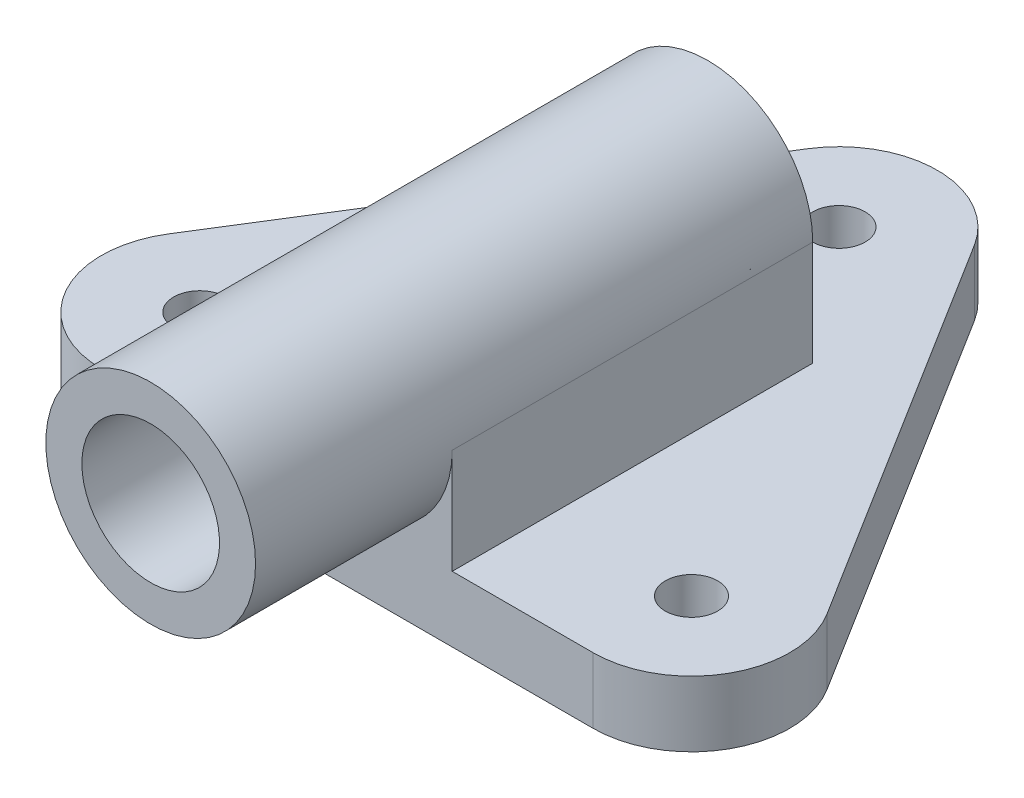
SolidWorks part; units mm, degrees
ref_plane "Front Plane" through (0, 0, 0) normal (0, 0, 1) x (1, 0, 0)
ref_plane "Top Plane" through (0, 0, 0) normal (0, 1, 0) x (1, 0, 0)
ref_plane "Right Plane" through (0, 0, 0) normal (1, 0, 0) x (0, 0, -1)
sketch "Sketch2" plane through (0, 0, 0) normal (0, 1, 0) x (1, 0, 0)
  line L0 (0, 0) -> (0, -4) construction
  line L1 (-50.22, -52.05) -> (-12.72, 7.95)
  line L2 (12.72, 7.95) -> (50.22, -52.05)
  line L3 (37.5, -75) -> (-37.5, -75)
  line L4 (0, -75) -> (0, -98.7993) construction
  arc A0 (12.72, 7.95) -> (-12.72, 7.95) centre (0, 0) ccw
  circle A1 centre (0, 0) radius 4
  arc A2 (-50.22, -52.05) -> (-37.5, -75) centre (-37.5, -60) ccw
  arc A3 (37.5, -75) -> (50.22, -52.05) centre (37.5, -60) ccw
  circle A4 centre (-37.5, -60) radius 4
  circle A5 centre (37.5, -60) radius 4
  dimension "D1" = 8
  dimension "D2" = 30
  dimension "D3" = 30
  dimension "D4" = 30
  dimension "D9" = 8
  dimension "D10" = 8
  dimension "D5" = 60
  dimension "D6" = 60
  dimension "D7" = 37.5
  dimension "D8" = 37.5
extrude "Boss-Extrude1" add sketch "Sketch2" along normal blind 10
sketch "Sketch3" plane through (0, 10, 0) normal (0, 1, 0) x (1, 0, 0)
  line L0 (-22.1183, -20) -> (22.244, -20) construction
  line L1 (-37.5, -75) -> (37.5, -75) construction
  dimension "D1" = 55
ref_plane "Plane1" through (0, 0, 20) normal (0, 0, 1) x (1, 0, 0)
sketch "Sketch4" plane through (0, 0, 20) normal (0, 0, 1) x (1, 0, 0)
  line L0 (-22.1183, 10) -> (22.244, 10) construction
  line L1 (16, 26) -> (16, 10)
  line L2 (16, 10) -> (-16, 10)
  line L3 (-16, 10) -> (-16, 26)
  arc A0 (16, 26) -> (-16, 26) centre (0, 26) ccw
  point P4 (0.0628, 10)
  dimension "D2" = 32
  dimension "D1" = 16
extrude "Boss-Extrude2" add sketch "Sketch4" along normal blind 85
sketch "Sketch5" plane through (0, 0, 20) normal (0, 0, -1) x (-1, 0, 0)
  circle A0 centre (0, 26) radius 10.5
  dimension "D1" = 21
extrude "Cut-Extrude1" cut sketch "Sketch5" against normal through all both and the other way through all
sketch "Sketch6" plane through (0, 0, 105) normal (0, 0, 1) x (1, 0, 0)
  line L0 (-16, 26) -> (-16, 10)
  line L1 (-16, 10) -> (16, 10) construction
  line L2 (-16, 10) -> (16, 10) construction
  line L3 (-16, 10) -> (16, 10)
  line L4 (16, 10) -> (16, 26)
  arc A0 (-16, 26) -> (16, 26) centre (0, 26) ccw
  line M4 (-16, 26) -> (-16, 10)
  line M5 (-16, 10) -> (16, 10)
  line M6 (16, 10) -> (16, 26)
extrude "Cut-Extrude2" cut sketch "Sketch6" against normal blind 30 contours A0 L3 M6 | A0 M4 M5
